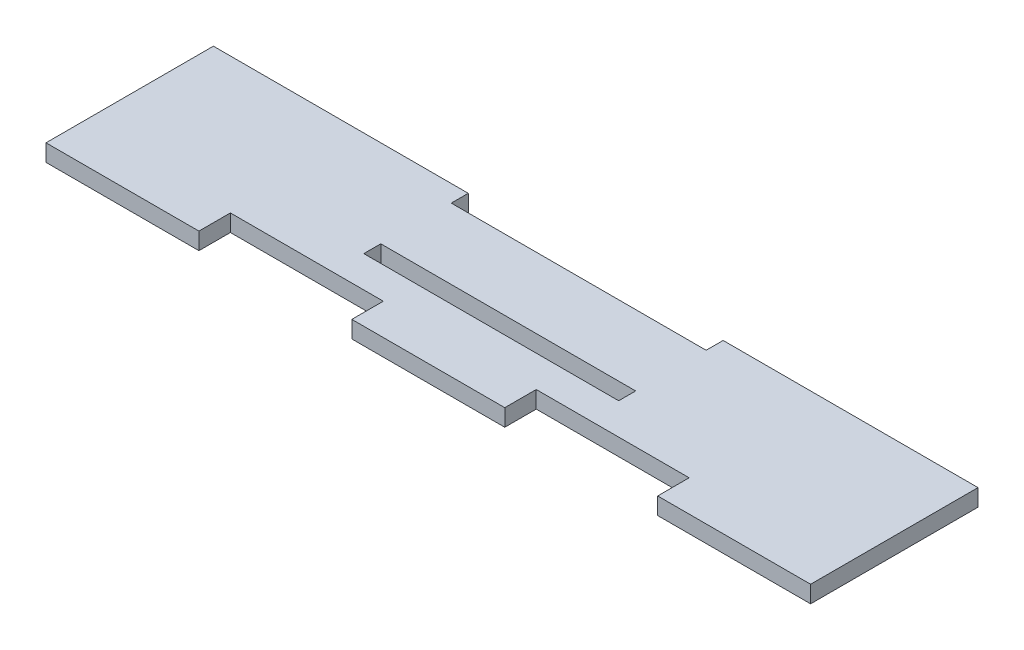
SolidWorks part; units mm, degrees
ref_plane "Front Plane" through (0, 0, 0) normal (0, 0, 1) x (1, 0, 0)
ref_plane "Top Plane" through (0, 0, 0) normal (0, 1, 0) x (1, 0, 0)
ref_plane "Right Plane" through (0, 0, 0) normal (1, 0, 0) x (0, 0, -1)
sketch "Sketch1" plane through (0, 0, 0) normal (0, 1, 0) x (1, 0, 0)
  line L0 (-20.25, -3.3) -> (20.25, -3.3)
  line L1 (-60.75, 13.3) -> (-20.25, 13.3)
  line L2 (-60.75, 13.3) -> (-60.75, -13.3)
  line L3 (-60.75, -13.3) -> (-36.45, -13.3)
  line L4 (60.75, 13.3) -> (60.75, -13.3)
  line L6 (-20.25, 10.6) -> (20.25, 10.6)
  line L7 (-20.25, -0.6) -> (20.25, -0.6)
  line L8 (-12.15, -13.3) -> (12.15, -13.3)
  line L11 (20.25, 13.3) -> (60.75, 13.3)
  line L12 (-20.25, 13.3) -> (-20.25, 10.6)
  line L13 (20.25, 13.3) -> (20.25, 10.6)
  line L14 (20.25, -0.6) -> (20.25, -3.3)
  line L15 (-20.25, -0.6) -> (-20.25, -3.3)
  line L16 (36.45, -13.3) -> (60.75, -13.3)
  line L17 (-36.45, -8.3) -> (-12.15, -8.3)
  line L18 (-36.45, -13.3) -> (-36.45, -8.3)
  line L19 (-12.15, -13.3) -> (-12.15, -8.3)
  line L20 (12.15, -13.3) -> (12.15, -8.3)
  line L21 (36.45, -13.3) -> (36.45, -8.3)
  line L22 (12.15, -8.3) -> (36.45, -8.3)
  point P0 (0, 0)
  dimension "D1" = 121.5
  dimension "D2" = 26.6
  dimension "D3" = 10
  dimension "D4" = 5
extrude "Boss-Extrude1" add sketch "Sketch1" along normal blind 2.7
